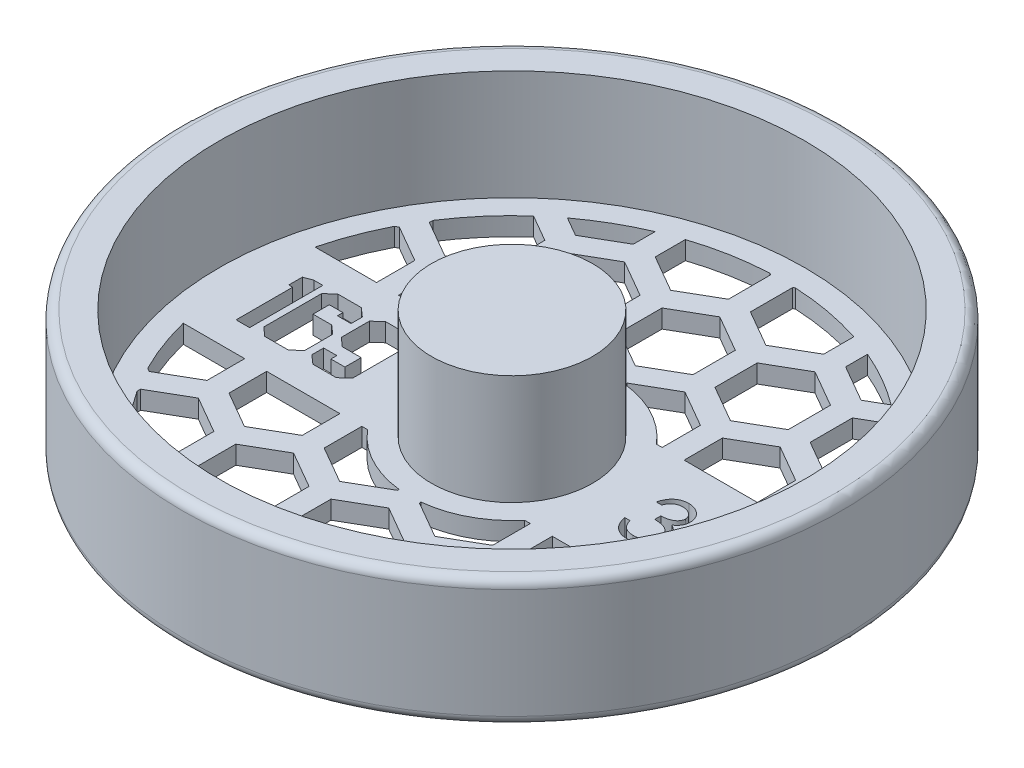
SolidWorks part; units mm, degrees
ref_plane "Front Plane" through (0, 0, 0) normal (0, 0, 1) x (1, 0, 0)
ref_plane "Top Plane" through (0, 0, 0) normal (0, 1, 0) x (1, 0, 0)
ref_plane "Right Plane" through (0, 0, 0) normal (1, 0, 0) x (0, 0, -1)
sketch "Sketch1" plane through (0, 0, 0) normal (0, 0, 1) x (1, 0, 0)
  line L0 (0, 0) -> (0, 22.225)
  line L1 (0, 22.225) -> (13.97, 22.225)
  line L2 (13.97, 22.225) -> (13.97, 3.175)
  line L3 (13.97, 3.175) -> (50.8, 3.175)
  line L4 (50.8, 3.175) -> (50.8, 22.225)
  line L5 (50.8, 22.225) -> (55.5625, 22.225)
  line L6 (57.15, 20.6375) -> (57.15, 1.5875)
  line L7 (55.5625, 0) -> (0, 0)
  arc A0 (55.5625, 0) -> (57.15, 1.5875) centre (55.5625, 1.5875) ccw
  arc A1 (57.15, 20.6375) -> (55.5625, 22.225) centre (55.5625, 20.6375) ccw
  dimension "D7" = 1.5875
  dimension "D1" = 50.8
  dimension "D2" = 3.175
  dimension "D3" = 6.35
  dimension "D4" = 13.97
  dimension "D5" = 19.05
  dimension "D6" = 19.05
revolve "Revolve1" add sketch "Sketch1" angle 360 about L0
sketch "Sketch3" plane through (0, 3.175, 0) normal (0, 1, 0) x (1, 0, 0)
  line L0 (-13.97, 0) -> (-50.8, 0) construction
  line L1 (-13.97, -6.35) -> (-50.8, -6.35) construction
  line L2 (13.97, 0) -> (50.8, 0) construction
  line L3 (13.97, -5.08) -> (50.8, -5.08) construction
  circle A0 centre (0, 0) radius 13.97 construction
  circle A1 centre (0, 0) radius 13.97 construction
  circle A2 centre (0, 0) radius 50.8 construction
  circle A3 centre (0, 0) radius 50.8 construction
  text T0 "169" font "Jersey M54" height 12.7
  text T1 "3/4" font "Century Gothic" height 10.16
  dimension "D1" = 6.35
  dimension "D2" = 5.08
extrude "Cut-Extrude2" cut sketch "Sketch3" against normal through all both and the other way through all
sketch "Sketch4" plane through (0, 3.175, 0) normal (0, 1, 0) x (1, 0, 0)
  line L0 (10.16, -3.6662) -> (16.51, -7.3323)
  line L1 (0, -7.3323) -> (6.35, -3.6662)
  line L2 (6.35, -3.6662) -> (6.35, 3.6662)
  line L3 (6.35, 3.6662) -> (0, 7.3323)
  line L4 (0, 7.3323) -> (-6.35, 3.6662)
  line L5 (-6.35, 3.6662) -> (-6.35, -3.6662)
  line L6 (-6.35, -3.6662) -> (0, -7.3323)
  line L7 (8.255, -21.6304) -> (14.605, -17.9643)
  line L8 (14.605, -17.9643) -> (14.605, -10.6319)
  line L9 (14.605, -10.6319) -> (8.255, -6.9657)
  line L10 (8.255, -6.9657) -> (1.905, -10.6319)
  line L11 (1.905, -10.6319) -> (1.905, -17.9643)
  line L12 (1.905, -17.9643) -> (8.255, -21.6304)
  line L13 (10.16, 3.6662) -> (10.16, -3.6662)
  line L14 (16.51, 7.3323) -> (10.16, 3.6662)
  line L15 (22.86, 3.6662) -> (16.51, 7.3323)
  line L16 (22.86, -3.6662) -> (22.86, 3.6662)
  line L17 (16.51, -7.3323) -> (22.86, -3.6662)
  line L18 (24.765, -21.6304) -> (31.115, -17.9643)
  line L19 (31.115, -17.9643) -> (31.115, -10.6319)
  line L20 (31.115, -10.6319) -> (24.765, -6.9657)
  line L21 (24.765, -6.9657) -> (18.415, -10.6319)
  line L22 (18.415, -10.6319) -> (18.415, -17.9643)
  line L23 (18.415, -17.9643) -> (24.765, -21.6304)
  line L24 (26.67, -3.6662) -> (33.02, -7.3323)
  line L25 (26.67, 3.6662) -> (26.67, -3.6662)
  line L26 (33.02, 7.3323) -> (26.67, 3.6662)
  line L27 (39.37, 3.6662) -> (33.02, 7.3323)
  line L28 (39.37, -3.6662) -> (39.37, 3.6662)
  line L29 (33.02, -7.3323) -> (39.37, -3.6662)
  line L30 (41.275, -21.6304) -> (47.625, -17.9643)
  line L31 (47.625, -17.9643) -> (47.625, -10.6319)
  line L32 (47.625, -10.6319) -> (41.275, -6.9657)
  line L33 (41.275, -6.9657) -> (34.925, -10.6319)
  line L34 (34.925, -10.6319) -> (34.925, -17.9643)
  line L35 (34.925, -17.9643) -> (41.275, -21.6304)
  line L36 (43.18, -3.6662) -> (49.53, -7.3323)
  line L37 (43.18, 3.6662) -> (43.18, -3.6662)
  line L38 (49.53, 7.3323) -> (43.18, 3.6662)
  line L39 (55.88, 3.6662) -> (49.53, 7.3323)
  line L40 (55.88, -3.6662) -> (55.88, 3.6662)
  line L41 (49.53, -7.3323) -> (55.88, -3.6662)
  line L42 (57.785, -21.6304) -> (64.135, -17.9643)
  line L43 (64.135, -17.9643) -> (64.135, -10.6319)
  line L44 (64.135, -10.6319) -> (57.785, -6.9657)
  line L45 (57.785, -6.9657) -> (51.435, -10.6319)
  line L46 (51.435, -10.6319) -> (51.435, -17.9643)
  line L47 (51.435, -17.9643) -> (57.785, -21.6304)
  line L48 (-22.86, -3.6662) -> (-16.51, -7.3323)
  line L49 (-22.86, 3.6662) -> (-22.86, -3.6662)
  line L50 (-16.51, 7.3323) -> (-22.86, 3.6662)
  line L51 (-10.16, 3.6662) -> (-16.51, 7.3323)
  line L52 (-10.16, -3.6662) -> (-10.16, 3.6662)
  line L53 (-16.51, -7.3323) -> (-10.16, -3.6662)
  line L54 (-8.255, -21.6304) -> (-1.905, -17.9643)
  line L55 (-1.905, -17.9643) -> (-1.905, -10.6319)
  line L56 (-1.905, -10.6319) -> (-8.255, -6.9657)
  line L57 (-8.255, -6.9657) -> (-14.605, -10.6319)
  line L58 (-14.605, -10.6319) -> (-14.605, -17.9643)
  line L59 (-14.605, -17.9643) -> (-8.255, -21.6304)
  line L60 (-39.37, -3.6662) -> (-33.02, -7.3323)
  line L61 (-39.37, 3.6662) -> (-39.37, -3.6662)
  line L62 (-33.02, 7.3323) -> (-39.37, 3.6662)
  line L63 (-26.67, 3.6662) -> (-33.02, 7.3323)
  line L64 (-26.67, -3.6662) -> (-26.67, 3.6662)
  line L65 (-33.02, -7.3323) -> (-26.67, -3.6662)
  line L66 (-24.765, -21.6304) -> (-18.415, -17.9643)
  line L67 (-18.415, -17.9643) -> (-18.415, -10.6319)
  line L68 (-18.415, -10.6319) -> (-24.765, -6.9657)
  line L69 (-24.765, -6.9657) -> (-31.115, -10.6319)
  line L70 (-31.115, -10.6319) -> (-31.115, -17.9643)
  line L71 (-31.115, -17.9643) -> (-24.765, -21.6304)
  line L72 (-55.88, -3.6662) -> (-49.53, -7.3323)
  line L73 (-55.88, 3.6662) -> (-55.88, -3.6662)
  line L74 (-49.53, 7.3323) -> (-55.88, 3.6662)
  line L75 (-43.18, 3.6662) -> (-49.53, 7.3323)
  line L76 (-43.18, -3.6662) -> (-43.18, 3.6662)
  line L77 (-49.53, -7.3323) -> (-43.18, -3.6662)
  line L78 (-41.275, -21.6304) -> (-34.925, -17.9643)
  line L79 (-34.925, -17.9643) -> (-34.925, -10.6319)
  line L80 (-34.925, -10.6319) -> (-41.275, -6.9657)
  line L81 (-41.275, -6.9657) -> (-47.625, -10.6319)
  line L82 (-47.625, -10.6319) -> (-47.625, -17.9643)
  line L83 (-47.625, -17.9643) -> (-41.275, -21.6304)
  line L84 (-6.35, 25.0358) -> (0, 21.3697)
  line L85 (-6.35, 32.3682) -> (-6.35, 25.0358)
  line L86 (0, 36.0343) -> (-6.35, 32.3682)
  line L87 (6.35, 32.3682) -> (0, 36.0343)
  line L88 (6.35, 25.0358) -> (6.35, 32.3682)
  line L89 (0, 21.3697) -> (6.35, 25.0358)
  line L90 (8.255, 7.0716) -> (14.605, 10.7377)
  line L91 (14.605, 10.7377) -> (14.605, 18.0701)
  line L92 (14.605, 18.0701) -> (8.255, 21.7363)
  line L93 (8.255, 21.7363) -> (1.905, 18.0701)
  line L94 (1.905, 18.0701) -> (1.905, 10.7377)
  line L95 (1.905, 10.7377) -> (8.255, 7.0716)
  line L96 (-8.255, 7.0716) -> (-1.905, 10.7377)
  line L97 (-1.905, 10.7377) -> (-1.905, 18.0701)
  line L98 (-1.905, 18.0701) -> (-8.255, 21.7363)
  line L99 (-8.255, 21.7363) -> (-14.605, 18.0701)
  line L100 (-14.605, 18.0701) -> (-14.605, 10.7377)
  line L101 (-14.605, 10.7377) -> (-8.255, 7.0716)
  line L102 (-22.86, 25.0358) -> (-16.51, 21.3697)
  line L103 (-16.51, 21.3697) -> (-10.16, 25.0358)
  line L104 (-10.16, 25.0358) -> (-10.16, 32.3682)
  line L105 (-10.16, 32.3682) -> (-16.51, 36.0343)
  line L106 (-16.51, 36.0343) -> (-22.86, 32.3682)
  line L107 (-22.86, 32.3682) -> (-22.86, 25.0358)
  line L108 (-24.765, 7.0716) -> (-18.415, 10.7377)
  line L109 (-18.415, 10.7377) -> (-18.415, 18.0701)
  line L110 (-18.415, 18.0701) -> (-24.765, 21.7363)
  line L111 (-24.765, 21.7363) -> (-31.115, 18.0701)
  line L112 (-31.115, 18.0701) -> (-31.115, 10.7377)
  line L113 (-31.115, 10.7377) -> (-24.765, 7.0716)
  line L114 (-39.37, 25.0358) -> (-33.02, 21.3697)
  line L115 (-33.02, 21.3697) -> (-26.67, 25.0358)
  line L116 (-26.67, 25.0358) -> (-26.67, 32.3682)
  line L117 (-26.67, 32.3682) -> (-33.02, 36.0343)
  line L118 (-33.02, 36.0343) -> (-39.37, 32.3682)
  line L119 (-39.37, 32.3682) -> (-39.37, 25.0358)
  line L120 (-55.88, 25.0358) -> (-49.53, 21.3697)
  line L121 (-49.53, 21.3697) -> (-43.18, 25.0358)
  line L122 (-43.18, 25.0358) -> (-43.18, 32.3682)
  line L123 (-43.18, 32.3682) -> (-49.53, 36.0343)
  line L124 (-49.53, 36.0343) -> (-55.88, 32.3682)
  line L125 (-55.88, 32.3682) -> (-55.88, 25.0358)
  line L126 (-41.275, 7.0716) -> (-34.925, 10.7377)
  line L127 (-34.925, 10.7377) -> (-34.925, 18.0701)
  line L128 (-34.925, 18.0701) -> (-41.275, 21.7363)
  line L129 (-41.275, 21.7363) -> (-47.625, 18.0701)
  line L130 (-47.625, 18.0701) -> (-47.625, 10.7377)
  line L131 (-47.625, 10.7377) -> (-41.275, 7.0716)
  line L132 (10.16, 25.0358) -> (16.51, 21.3697)
  line L133 (16.51, 21.3697) -> (22.86, 25.0358)
  line L134 (22.86, 25.0358) -> (22.86, 32.3682)
  line L135 (22.86, 32.3682) -> (16.51, 36.0343)
  line L136 (16.51, 36.0343) -> (10.16, 32.3682)
  line L137 (10.16, 32.3682) -> (10.16, 25.0358)
  line L138 (24.765, 7.0716) -> (31.115, 10.7377)
  line L139 (31.115, 10.7377) -> (31.115, 18.0701)
  line L140 (31.115, 18.0701) -> (24.765, 21.7363)
  line L141 (24.765, 21.7363) -> (18.415, 18.0701)
  line L142 (18.415, 18.0701) -> (18.415, 10.7377)
  line L143 (18.415, 10.7377) -> (24.765, 7.0716)
  line L144 (26.67, 25.0358) -> (33.02, 21.3697)
  line L145 (33.02, 21.3697) -> (39.37, 25.0358)
  line L146 (39.37, 25.0358) -> (39.37, 32.3682)
  line L147 (39.37, 32.3682) -> (33.02, 36.0343)
  line L148 (33.02, 36.0343) -> (26.67, 32.3682)
  line L149 (26.67, 32.3682) -> (26.67, 25.0358)
  line L150 (41.275, 7.0716) -> (47.625, 10.7377)
  line L151 (47.625, 10.7377) -> (47.625, 18.0701)
  line L152 (47.625, 18.0701) -> (41.275, 21.7363)
  line L153 (41.275, 21.7363) -> (34.925, 18.0701)
  line L154 (34.925, 18.0701) -> (34.925, 10.7377)
  line L155 (34.925, 10.7377) -> (41.275, 7.0716)
  line L156 (43.18, 25.0358) -> (49.53, 21.3697)
  line L157 (49.53, 21.3697) -> (55.88, 25.0358)
  line L158 (55.88, 25.0358) -> (55.88, 32.3682)
  line L159 (55.88, 32.3682) -> (49.53, 36.0343)
  line L160 (49.53, 36.0343) -> (43.18, 32.3682)
  line L161 (43.18, 32.3682) -> (43.18, 25.0358)
  line L162 (57.785, 7.0716) -> (64.135, 10.7377)
  line L163 (64.135, 10.7377) -> (64.135, 18.0701)
  line L164 (64.135, 18.0701) -> (57.785, 21.7363)
  line L165 (57.785, 21.7363) -> (51.435, 18.0701)
  line L166 (51.435, 18.0701) -> (51.435, 10.7377)
  line L167 (51.435, 10.7377) -> (57.785, 7.0716)
  line L168 (-6.35, 53.7378) -> (0, 50.0717)
  line L169 (-6.35, 61.0702) -> (-6.35, 53.7378)
  line L170 (0, 64.7363) -> (-6.35, 61.0702)
  line L171 (6.35, 61.0702) -> (0, 64.7363)
  line L172 (6.35, 53.7378) -> (6.35, 61.0702)
  line L173 (0, 50.0717) -> (6.35, 53.7378)
  line L174 (8.255, 35.7736) -> (14.605, 39.4397)
  line L175 (14.605, 39.4397) -> (14.605, 46.7721)
  line L176 (14.605, 46.7721) -> (8.255, 50.4383)
  line L177 (8.255, 50.4383) -> (1.905, 46.7721)
  line L178 (1.905, 46.7721) -> (1.905, 39.4397)
  line L179 (1.905, 39.4397) -> (8.255, 35.7736)
  line L180 (-8.255, 35.7736) -> (-1.905, 39.4397)
  line L181 (-1.905, 39.4397) -> (-1.905, 46.7721)
  line L182 (-1.905, 46.7721) -> (-8.255, 50.4383)
  line L183 (-8.255, 50.4383) -> (-14.605, 46.7721)
  line L184 (-14.605, 46.7721) -> (-14.605, 39.4397)
  line L185 (-14.605, 39.4397) -> (-8.255, 35.7736)
  line L186 (-22.86, 53.7378) -> (-16.51, 50.0717)
  line L187 (-16.51, 50.0717) -> (-10.16, 53.7378)
  line L188 (-10.16, 53.7378) -> (-10.16, 61.0702)
  line L189 (-10.16, 61.0702) -> (-16.51, 64.7363)
  line L190 (-16.51, 64.7363) -> (-22.86, 61.0702)
  line L191 (-22.86, 61.0702) -> (-22.86, 53.7378)
  line L192 (-24.765, 35.7736) -> (-18.415, 39.4397)
  line L193 (-18.415, 39.4397) -> (-18.415, 46.7721)
  line L194 (-18.415, 46.7721) -> (-24.765, 50.4383)
  line L195 (-24.765, 50.4383) -> (-31.115, 46.7721)
  line L196 (-31.115, 46.7721) -> (-31.115, 39.4397)
  line L197 (-31.115, 39.4397) -> (-24.765, 35.7736)
  line L198 (-39.37, 53.7378) -> (-33.02, 50.0717)
  line L199 (-33.02, 50.0717) -> (-26.67, 53.7378)
  line L200 (-26.67, 53.7378) -> (-26.67, 61.0702)
  line L201 (-26.67, 61.0702) -> (-33.02, 64.7363)
  line L202 (-33.02, 64.7363) -> (-39.37, 61.0702)
  line L203 (-39.37, 61.0702) -> (-39.37, 53.7378)
  line L204 (-55.88, 53.7378) -> (-49.53, 50.0717)
  line L205 (-49.53, 50.0717) -> (-43.18, 53.7378)
  line L206 (-43.18, 53.7378) -> (-43.18, 61.0702)
  line L207 (-43.18, 61.0702) -> (-49.53, 64.7363)
  line L208 (-49.53, 64.7363) -> (-55.88, 61.0702)
  line L209 (-55.88, 61.0702) -> (-55.88, 53.7378)
  line L210 (-41.275, 35.7736) -> (-34.925, 39.4397)
  line L211 (-34.925, 39.4397) -> (-34.925, 46.7721)
  line L212 (-34.925, 46.7721) -> (-41.275, 50.4383)
  line L213 (-41.275, 50.4383) -> (-47.625, 46.7721)
  line L214 (-47.625, 46.7721) -> (-47.625, 39.4397)
  line L215 (-47.625, 39.4397) -> (-41.275, 35.7736)
  line L216 (10.16, 53.7378) -> (16.51, 50.0717)
  line L217 (16.51, 50.0717) -> (22.86, 53.7378)
  line L218 (22.86, 53.7378) -> (22.86, 61.0702)
  line L219 (22.86, 61.0702) -> (16.51, 64.7363)
  line L220 (16.51, 64.7363) -> (10.16, 61.0702)
  line L221 (10.16, 61.0702) -> (10.16, 53.7378)
  line L222 (24.765, 35.7736) -> (31.115, 39.4397)
  line L223 (31.115, 39.4397) -> (31.115, 46.7721)
  line L224 (31.115, 46.7721) -> (24.765, 50.4383)
  line L225 (24.765, 50.4383) -> (18.415, 46.7721)
  line L226 (18.415, 46.7721) -> (18.415, 39.4397)
  line L227 (18.415, 39.4397) -> (24.765, 35.7736)
  line L228 (26.67, 53.7378) -> (33.02, 50.0717)
  line L229 (33.02, 50.0717) -> (39.37, 53.7378)
  line L230 (39.37, 53.7378) -> (39.37, 61.0702)
  line L231 (39.37, 61.0702) -> (33.02, 64.7363)
  line L232 (33.02, 64.7363) -> (26.67, 61.0702)
  line L233 (26.67, 61.0702) -> (26.67, 53.7378)
  line L234 (41.275, 35.7736) -> (47.625, 39.4397)
  line L235 (47.625, 39.4397) -> (47.625, 46.7721)
  line L236 (47.625, 46.7721) -> (41.275, 50.4383)
  line L237 (41.275, 50.4383) -> (34.925, 46.7721)
  line L238 (34.925, 46.7721) -> (34.925, 39.4397)
  line L239 (34.925, 39.4397) -> (41.275, 35.7736)
  line L240 (43.18, 53.7378) -> (49.53, 50.0717)
  line L241 (49.53, 50.0717) -> (55.88, 53.7378)
  line L242 (55.88, 53.7378) -> (55.88, 61.0702)
  line L243 (55.88, 61.0702) -> (49.53, 64.7363)
  line L244 (49.53, 64.7363) -> (43.18, 61.0702)
  line L245 (43.18, 61.0702) -> (43.18, 53.7378)
  line L246 (57.785, 35.7736) -> (64.135, 39.4397)
  line L247 (64.135, 39.4397) -> (64.135, 46.7721)
  line L248 (64.135, 46.7721) -> (57.785, 50.4383)
  line L249 (57.785, 50.4383) -> (51.435, 46.7721)
  line L250 (51.435, 46.7721) -> (51.435, 39.4397)
  line L251 (51.435, 39.4397) -> (57.785, 35.7736)
  line L252 (-6.35, -32.3682) -> (0, -36.0343)
  line L253 (-6.35, -25.0358) -> (-6.35, -32.3682)
  line L254 (0, -21.3697) -> (-6.35, -25.0358)
  line L255 (6.35, -25.0358) -> (0, -21.3697)
  line L256 (6.35, -32.3682) -> (6.35, -25.0358)
  line L257 (0, -36.0343) -> (6.35, -32.3682)
  line L258 (8.255, -50.3324) -> (14.605, -46.6663)
  line L259 (14.605, -46.6663) -> (14.605, -39.3339)
  line L260 (14.605, -39.3339) -> (8.255, -35.6677)
  line L261 (8.255, -35.6677) -> (1.905, -39.3339)
  line L262 (1.905, -39.3339) -> (1.905, -46.6663)
  line L263 (1.905, -46.6663) -> (8.255, -50.3324)
  line L264 (-8.255, -50.3324) -> (-1.905, -46.6663)
  line L265 (-1.905, -46.6663) -> (-1.905, -39.3339)
  line L266 (-1.905, -39.3339) -> (-8.255, -35.6677)
  line L267 (-8.255, -35.6677) -> (-14.605, -39.3339)
  line L268 (-14.605, -39.3339) -> (-14.605, -46.6663)
  line L269 (-14.605, -46.6663) -> (-8.255, -50.3324)
  line L270 (-22.86, -32.3682) -> (-16.51, -36.0343)
  line L271 (-16.51, -36.0343) -> (-10.16, -32.3682)
  line L272 (-10.16, -32.3682) -> (-10.16, -25.0358)
  line L273 (-10.16, -25.0358) -> (-16.51, -21.3697)
  line L274 (-16.51, -21.3697) -> (-22.86, -25.0358)
  line L275 (-22.86, -25.0358) -> (-22.86, -32.3682)
  line L276 (-24.765, -50.3324) -> (-18.415, -46.6663)
  line L277 (-18.415, -46.6663) -> (-18.415, -39.3339)
  line L278 (-18.415, -39.3339) -> (-24.765, -35.6677)
  line L279 (-24.765, -35.6677) -> (-31.115, -39.3339)
  line L280 (-31.115, -39.3339) -> (-31.115, -46.6663)
  line L281 (-31.115, -46.6663) -> (-24.765, -50.3324)
  line L282 (-39.37, -32.3682) -> (-33.02, -36.0343)
  line L283 (-33.02, -36.0343) -> (-26.67, -32.3682)
  line L284 (-26.67, -32.3682) -> (-26.67, -25.0358)
  line L285 (-26.67, -25.0358) -> (-33.02, -21.3697)
  line L286 (-33.02, -21.3697) -> (-39.37, -25.0358)
  line L287 (-39.37, -25.0358) -> (-39.37, -32.3682)
  line L288 (-55.88, -32.3682) -> (-49.53, -36.0343)
  line L289 (-49.53, -36.0343) -> (-43.18, -32.3682)
  line L290 (-43.18, -32.3682) -> (-43.18, -25.0358)
  line L291 (-43.18, -25.0358) -> (-49.53, -21.3697)
  line L292 (-49.53, -21.3697) -> (-55.88, -25.0358)
  line L293 (-55.88, -25.0358) -> (-55.88, -32.3682)
  line L294 (-41.275, -50.3324) -> (-34.925, -46.6663)
  line L295 (-34.925, -46.6663) -> (-34.925, -39.3339)
  line L296 (-34.925, -39.3339) -> (-41.275, -35.6677)
  line L297 (-41.275, -35.6677) -> (-47.625, -39.3339)
  line L298 (-47.625, -39.3339) -> (-47.625, -46.6663)
  line L299 (-47.625, -46.6663) -> (-41.275, -50.3324)
  line L300 (10.16, -32.3682) -> (16.51, -36.0343)
  line L301 (16.51, -36.0343) -> (22.86, -32.3682)
  line L302 (22.86, -32.3682) -> (22.86, -25.0358)
  line L303 (22.86, -25.0358) -> (16.51, -21.3697)
  line L304 (16.51, -21.3697) -> (10.16, -25.0358)
  line L305 (10.16, -25.0358) -> (10.16, -32.3682)
  line L306 (24.765, -50.3324) -> (31.115, -46.6663)
  line L307 (31.115, -46.6663) -> (31.115, -39.3339)
  line L308 (31.115, -39.3339) -> (24.765, -35.6677)
  line L309 (24.765, -35.6677) -> (18.415, -39.3339)
  line L310 (18.415, -39.3339) -> (18.415, -46.6663)
  line L311 (18.415, -46.6663) -> (24.765, -50.3324)
  line L312 (26.67, -32.3682) -> (33.02, -36.0343)
  line L313 (33.02, -36.0343) -> (39.37, -32.3682)
  line L314 (39.37, -32.3682) -> (39.37, -25.0358)
  line L315 (39.37, -25.0358) -> (33.02, -21.3697)
  line L316 (33.02, -21.3697) -> (26.67, -25.0358)
  line L317 (26.67, -25.0358) -> (26.67, -32.3682)
  line L318 (41.275, -50.3324) -> (47.625, -46.6663)
  line L319 (47.625, -46.6663) -> (47.625, -39.3339)
  line L320 (47.625, -39.3339) -> (41.275, -35.6677)
  line L321 (41.275, -35.6677) -> (34.925, -39.3339)
  line L322 (34.925, -39.3339) -> (34.925, -46.6663)
  line L323 (34.925, -46.6663) -> (41.275, -50.3324)
  line L324 (43.18, -32.3682) -> (49.53, -36.0343)
  line L325 (49.53, -36.0343) -> (55.88, -32.3682)
  line L326 (55.88, -32.3682) -> (55.88, -25.0358)
  line L327 (55.88, -25.0358) -> (49.53, -21.3697)
  line L328 (49.53, -21.3697) -> (43.18, -25.0358)
  line L329 (43.18, -25.0358) -> (43.18, -32.3682)
  line L330 (57.785, -50.3324) -> (64.135, -46.6663)
  line L331 (64.135, -46.6663) -> (64.135, -39.3339)
  line L332 (64.135, -39.3339) -> (57.785, -35.6677)
  line L333 (57.785, -35.6677) -> (51.435, -39.3339)
  line L334 (51.435, -39.3339) -> (51.435, -46.6663)
  line L335 (51.435, -46.6663) -> (57.785, -50.3324)
  line L336 (0, -11.43) -> (0, 11.43)
  line L337 (52.0496, 11.43) -> (-52.0496, 11.43)
  line L338 (52.0496, -11.43) -> (-52.0496, -11.43)
  line L339 (-52.0496, 11.43) -> (-52.0496, -11.43)
  line L340 (52.0496, 11.43) -> (52.0496, -11.43)
  circle A0 centre (0, 0) radius 6.35 construction
  circle A1 centre (8.255, -14.2981) radius 6.35 construction
  circle A2 centre (0, 0) radius 46.99
  circle A3 centre (0, 0) radius 17.78
  point P18 (3.175, -5.4993)
  point P345 (0, 0)
  point P348 (0, 11.43)
  point P351 (0, -11.43)
  dimension "D10" = 93.98
  dimension "D11" = 35.56
  dimension "D1" = 12.7
  dimension "D2" = 12.7
  dimension "D3" = 3.81
  dimension "D4" = 1.905
  dimension "D9" = 22.86
  dimension "D5" = 4
  dimension "D6" = 4
  dimension "D7" = 3
  dimension "D8" = 2
extrude "Cut-Extrude4" cut sketch "Sketch4" against normal through all both and the other way through all contours L129 A2 L337 L127 L128 | L337 L109 L110 L111 L112 | L117 A2 L119 L114 L115 L116 | L193 A2 L197 L192 | L106 L107 L102 L103 L104 L105 | L182 A2 L184 L185 L180 L181 | L84 L89 L88 L87 L86 L85 | A3 L97 L98 L99 L100 L337 | A3 L337 L91 L92 L93 L94 | L175 A2 L177 L178 L179 L174 | L136 L137 L132 L133 L134 L135 | L222 A2 L226 L227 | L146 A2 L148 L149 L144 L145 | L337 L139 L140 L141 L142 | L337 A2 L152 L153 L154 | L30 A2 L338 L34 L35 | L19 L338 L22 L23 L18 | A3 L11 L12 L7 L8 L338 | L312 A2 L314 L315 L316 L317 | L310 A2 L308 L309 | L304 L305 L300 L301 L302 L303 | L263 A2 L259 L260 L261 L262 | L252 L257 L256 L255 L254 L253 | L268 A2 L264 L265 L266 L267 | L274 L275 L270 L271 L272 L273 | L279 A2 L277 L278 | L287 A2 L283 L284 L285 L286 | L338 A2 L83 L78 L79 | L67 L338 L70 L71 L66 | A3 L338 L58 L59 L54 L55
